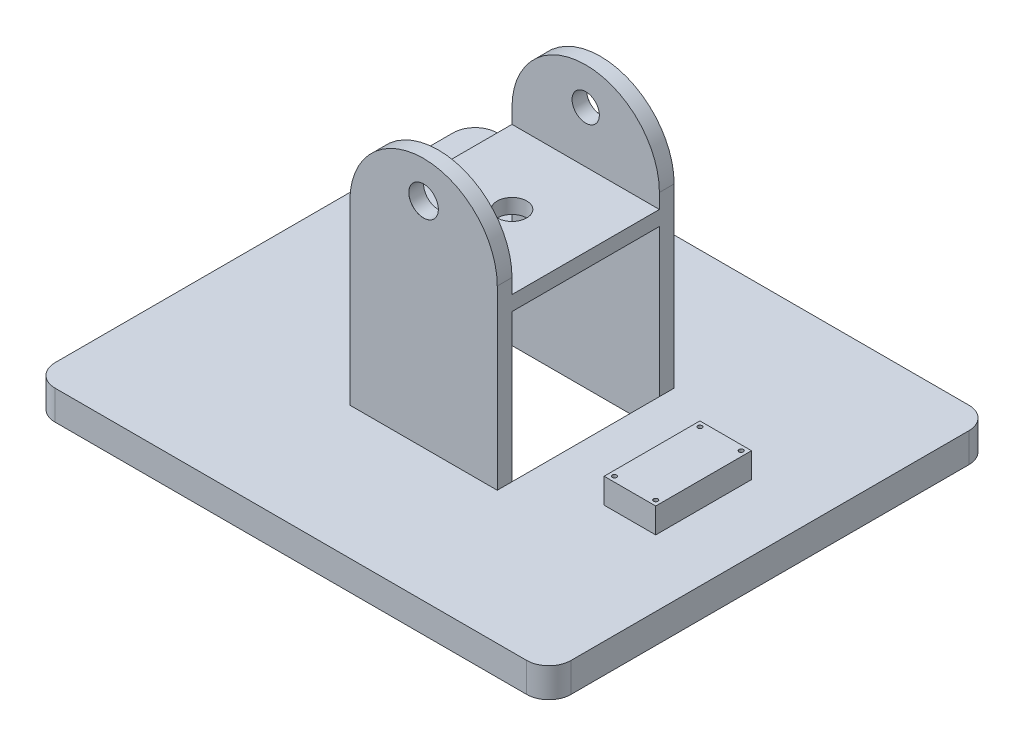
SolidWorks part; units mm, degrees
ref_plane "Front Plane" through (0, 0, 0) normal (0, 0, 1) x (1, 0, 0)
ref_plane "Top Plane" through (0, 0, 0) normal (0, 1, 0) x (1, 0, 0)
ref_plane "Right Plane" through (0, 0, 0) normal (1, 0, 0) x (0, 0, -1)
sketch "Sketch1" plane through (0, 0, 0) normal (0, 1, 0) x (1, 0, 0)
  line L1 (0, 0) -> (350, 0)
  line L2 (0, 0) -> (0, -300)
  line L3 (0, -300) -> (350, -300)
  line L4 (350, 0) -> (350, -300)
  dimension "D1" = 350
  dimension "D2" = 300
extrude "Boss-Extrude1" add sketch "Sketch1" along normal blind 20
fillet "Fillet1" radius 15 4 edges at (350, 10, 0) (0, 10, 0) (0, 10, 300) (350, 10, 300)
sketch "Sketch2" plane through (0, 20, 0) normal (0, 1, 0) x (1, 0, 0)
  line L0 (335, 0) -> (15, 0) construction
  line L1 (125, -100) -> (225, -100)
  line L2 (125, -100) -> (125, -200)
  line L3 (125, -200) -> (225, -200)
  line L4 (225, -100) -> (225, -200)
  line L8 (175, -100) -> (175, 0) construction
  line L9 (175, -200) -> (175, -300) construction
  line L10 (15, -300) -> (335, -300) construction
  line L11 (125, -150) -> (0, -150) construction
  line L12 (0, -15) -> (0, -285) construction
  line L13 (225, -150) -> (350, -150) construction
  line L14 (350, -285) -> (350, -15) construction
  dimension "D2" = 100
  dimension "D1" = 100
extrude "Cut-Extrude1" cut sketch "Sketch2" against normal blind 20 contours L1 L4 L3 L2
sketch "Sketch6" plane through (0, 0, 100) normal (0, 0, 1) x (1, 0, 0)
  line L0 (125, 0) -> (125, 140)
  line L1 (225, 140) -> (225, 0)
  line L2 (15, 0) -> (335, 0) construction
  line L3 (125, 140) -> (225, 140) construction
  line L4 (125, 0) -> (225, 0)
  arc A0 (125, 140) -> (225, 140) centre (175, 140) cw
  dimension "D1" = 100
  dimension "D2" = 140
extrude "Boss-Extrude2" add sketch "Sketch6" against normal blind 10
pattern_linear "LPattern1" count 2 spacing 110 along (0, 0, 1) of "Boss-Extrude2"
sketch "Sketch23" plane through (0, 0, 210) normal (0, 0, 1) x (1, 0, 0)
  line L0 (125, 140) -> (225, 140) construction
  line L1 (225, 140) -> (175, 140) construction
  line L2 (175, 140) -> (175, 190) construction
  line L3 (175, 190) -> (175, 165) construction
  line L4 (175, 165) -> (218.3013, 165) construction
  arc A0 (225, 140) -> (125, 140) centre (175, 140) ccw construction
hole_wizard "Ø20.0 (20) Diameter Hole2" positions "Sketch24" profile "Sketch25" hole size "Ø20.0" standard "ANSI Metric"
sketch "Sketch24" plane through (0, 0, 210) normal (0, 0, 1) x (1, 0, 0)
  point P0 (175, 165)
sketch "Sketch25" plane through (175, 165, 210) normal (1, 0, 0) x (0, -1, 0)
  line L0 (0, 0) -> (0, 16.0086)
  line L1 (0, 16.0086) -> (10, 10)
  line L2 (10, 10) -> (10, 0.025)
  line L3 (10, 0.025) -> (10.025, 0)
  line L5 (10.025, 0) -> (0, 0)
  line L6 (-10, 0.025) -> (-10.025, 0) construction
  line L10 (0, 16.0086) -> (-10, 10) construction
  line L11 (0, -6.35) -> (0, 107.95) construction
  dimension "Hole Dia." = 20
  dimension "Hole Depth" = 10
  dimension "Near C'Sink Dia." = 20.05
  dimension "Near C'Sink Angle" = 90
  dimension "Drill Angle" = 118
hole_wizard "Ø18.5 (18.5) Diameter Hole1" positions "Sketch29" profile "Sketch30" hole size "Ø18.5" standard "ANSI Metric"
sketch "Sketch29" plane through (0, 0, 90) normal (0, 0, -1) x (-1, 0, 0)
  point P0 (-175, 165)
sketch "Sketch30" plane through (175, 165, 90) normal (1, 0, 0) x (0, 1, 0)
  line L0 (0, 0) -> (0, 15.558)
  line L1 (0, 15.558) -> (9.25, 10)
  line L2 (9.25, 10) -> (9.25, 0.025)
  line L3 (9.25, 0.025) -> (9.275, 0)
  line L5 (9.275, 0) -> (0, 0)
  line L6 (-9.25, 0.025) -> (-9.275, 0) construction
  line L10 (0, 15.558) -> (-9.25, 10) construction
  line L11 (0, -6.35) -> (0, 107.95) construction
  dimension "Hole Dia." = 18.5
  dimension "Hole Depth" = 10
  dimension "Near C'Sink Dia." = 18.55
  dimension "Near C'Sink Angle" = 90
  dimension "Drill Angle" = 118
sketch "Sketch32" plane through (0, 0, 210) normal (0, 0, 1) x (1, 0, 0)
  line L0 (125, 140) -> (125, 20) construction
  line L16 (125, 130) -> (225, 130)
  line L17 (125, 130) -> (125, 120)
  line L18 (125, 120) -> (225, 120)
  line L19 (225, 130) -> (225, 120)
  line L20 (225, 20) -> (225, 140) construction
  line L21 (225, 20) -> (125, 20) construction
  dimension "D1" = 100
extrude "Boss-Extrude3" add sketch "Sketch32" against normal blind 120
sketch "Sketch37" plane through (0, 130, 0) normal (0, 1, 0) x (1, 0, 0)
  line L0 (175, -90) -> (175, -210) construction
  line L1 (225, -90) -> (125, -90) construction
  line L2 (125, -210) -> (225, -210) construction
  line L3 (175, -210) -> (175, -150) construction
  line L4 (175, -150) -> (225, -150) construction
  line L5 (225, -100) -> (225, -200) construction
  line L6 (225, -150) -> (125, -150) construction
  line L7 (125, -100) -> (125, -200) construction
  circle A0 centre (175, -150) radius 10
  dimension "D1" = 20
extrude "Cut-Extrude2" cut sketch "Sketch37" against normal blind 36.0783
sketch "Sketch45" plane through (0, 20, 0) normal (0, 1, 0) x (1, 0, 0)
  line L0 (287.5, -117.5) -> (287.5, 0) construction
  line L1 (270, -117.5) -> (305, -117.5)
  line L2 (270, -117.5) -> (270, -182.5)
  line L3 (270, -182.5) -> (305, -182.5)
  line L4 (305, -117.5) -> (305, -182.5)
  line L5 (335, 0) -> (15, 0) construction
  line L6 (287.5, -182.5) -> (287.5, -300) construction
  line L7 (15, -300) -> (335, -300) construction
  line L8 (270, -150) -> (225, -150) construction
  line L9 (225, -100) -> (225, -200) construction
  line L10 (305, -150) -> (350, -150) construction
  line L11 (350, -285) -> (350, -15) construction
  dimension "D1" = 65
  dimension "D2" = 35
extrude "Boss-Extrude4" add sketch "Sketch45" along normal blind 17 contours L4 L3 L2 L1
hole_wizard "M2.5 Clearance Hole1" positions "Sketch50" profile "Sketch51" hole size "M2.5" standard "ISO"
sketch "Sketch50" plane through (0, 37, 0) normal (0, 1, 0) x (1, 0, 0)
  line L0 (270, -117.5) -> (305, -117.5) construction
  line L1 (270, -117.5) -> (270, -182.5) construction
  line L2 (270, -117.5) -> (305, -117.5) construction
  line L3 (305, -117.5) -> (305, -182.5) construction
  line L4 (270, -182.5) -> (305, -182.5) construction
  point P0 (273.5, -121)
  point P2 (301.5, -121)
  point P3 (301.5, -179)
  point P5 (273.5, -179)
  dimension "D1" = 3.5
  dimension "D3" = 3.5
  dimension "D4" = 3.5
  dimension "D5" = 3.5
  dimension "D6" = 3.5
  dimension "D7" = 3.5
  dimension "D8" = 3.5
sketch "Sketch51" plane through (273.5, 37, 121) normal (1, 0, 0) x (0, 0, 1)
  line L0 (0, 0) -> (0, 13.2712)
  line L1 (0, 13.2712) -> (1.45, 12.4)
  line L2 (1.45, 12.4) -> (1.45, 0.025)
  line L3 (1.45, 0.025) -> (1.475, 0)
  line L5 (1.475, 0) -> (0, 0)
  line L6 (-1.45, 0.025) -> (-1.475, 0) construction
  line L10 (0, 13.2712) -> (-1.45, 12.4) construction
  line L11 (0, -6.35) -> (0, 107.95) construction
  dimension "Hole Dia." = 2.9
  dimension "Hole Depth" = 12.4
  dimension "Near C'Sink Dia." = 2.95
  dimension "Near C'Sink Angle" = 90
  dimension "Drill Angle" = 118
equation "\"bar_width\"=100"
equation "\"D2@Sketch2\"=\"bar_width\""
equation "\"bar_length\"=100"
equation "\"D1@Sketch2\"=\"bar_length\""
equation "\"D1@Boss-Extrude3\"=\"bar_length\" + 20mm"
equation "\"tower-height\"=100"
equation "\"D1@Sketch32\"=\"tower-height\""
equation "\"lens_diameter\"=20"
equation "\"D1@Sketch37\"=\"lens_diameter\""
equation "\"R_pi_length\"=65"
equation "\"D1@Sketch45\"=\"R_pi_length\""
equation "\"R_pi_width\"=35"
equation "\"D2@Sketch45\"=\"R_pi_width\""
equation "\"RP_tappings\"=3.5"
equation "\"D1@Sketch50\"=\"RP_tappings\""
